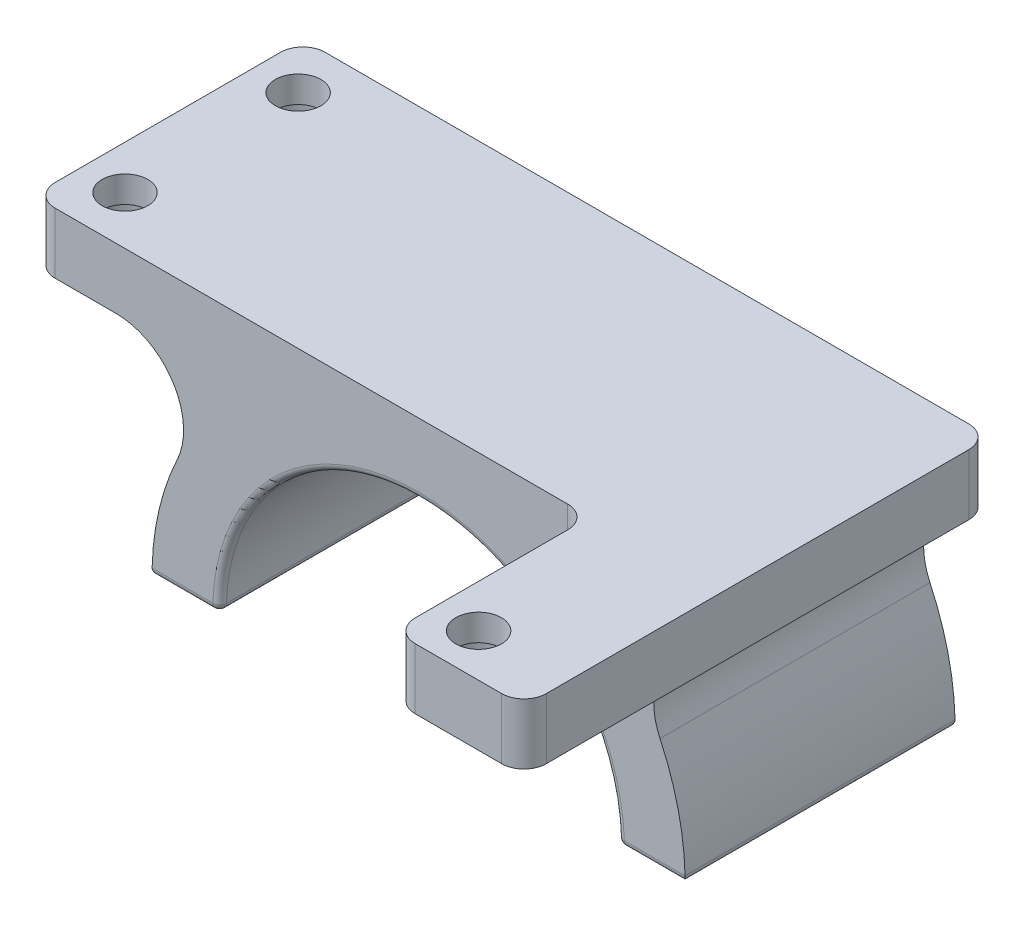
SolidWorks part; units mm, degrees
ref_plane "Front Plane" through (0, 0, 0) normal (0, 0, 1) x (1, 0, 0)
ref_plane "Top Plane" through (0, 0, 0) normal (0, 1, 0) x (1, 0, 0)
ref_plane "Right Plane" through (0, 0, 0) normal (1, 0, 0) x (0, 0, -1)
sketch "Sketch1" plane through (0, 0, 0) normal (0, 0, 1) x (1, 0, 0)
  circle A0 centre (0, 0) radius 39.5
  dimension "D1" = 79
extrude "Boss-Extrude1" add sketch "Sketch1" along normal blind 40 contours A0
sketch "Sketch2" plane through (0, 0, 0) normal (0, 0, -1) x (-1, 0, 0)
  line L0 (-39.5, 0) -> (39.5, 0)
  circle A0 centre (0, 0) radius 39.5 construction
  arc A2 (39.5, 0) -> (-39.5, 0) centre (0, 0) cw
extrude "Cut-Extrude2" cut sketch "Sketch2" against normal through all contours A2 L0
sketch "Sketch3" plane through (0, 0, 0) normal (0, 0, -1) x (-1, 0, 0)
  line L0 (-39.5, 0) -> (39.5, 0) construction
  line L1 (-29.5, 0) -> (29.5, 0)
  arc A0 (-29.5, 0) -> (29.5, 0) centre (0, 0) cw
  dimension "D1" = 29.5
extrude "Cut-Extrude3" cut sketch "Sketch3" against normal through all
fillet "Fillet2" radius 1 10 edges at (29.5, 0, 20) (-29.5, 0, 20) (0, 29.5, 40) (0, 29.5, 0) (-39.5, 0, 20) (39.5, 0, 20) (34.5, 0, 40) (-34.5, 0, 40) (34.5, 0, 0) (-34.5, 0, 0)
sketch "Sketch6" plane through (0, 0, 0) normal (0, 0, -1) x (-1, 0, 0)
  line L5 (-57.15, 40) -> (57.15, 40)
  line L6 (-57.15, 40) -> (-57.15, 31)
  line L7 (-57.15, 31) -> (57.15, 31)
  line L8 (57.15, 40) -> (57.15, 31)
  arc A0 (39.4867, 1.026) -> (-39.4867, 1.026) centre (0, 0) ccw construction
  point P9 (0, 39.5)
  point P10 (0, 31)
  dimension "D3" = 40
  dimension "D1" = 9
  dimension "D2" = 114.3
extrude "Boss-Extrude2" add sketch "Sketch6" against normal up to surface (40 mm away) up to face at (0, 12.3377, 40)
fillet "Fillet6" radius 10 2 edges at (-24.4796, 31, 20) (24.4796, 31, 20)
ref_plane "Plane1" through (-44.8247, 31, 0) normal (-1, 0, 0) x (0, 0, 1)
sketch "Sketch9" plane through (0, 40, 0) normal (0, 1, 0) x (1, 0, 0)
  line L1 (-50.6774, -7.173) -> (-50.6774, -3.7948) construction
  line L4 (-57.15, -40) -> (-57.15, 0) construction
  line L5 (-50.6774, -7.173) -> (-50.6774, -32.827) construction
  circle A0 centre (-50.6774, -7.173) radius 3.3782
  circle A1 centre (-50.6774, -32.827) radius 3.3782
  point P5 (-50.6774, -20)
  point P6 (-57.15, -20)
  dimension "D1" = 6.7564
  dimension "D2" = 6.4726
  dimension "D3" = 2
extrude "Cut-Extrude4" cut sketch "Sketch9" against normal up to surface (10.8916 mm away)
sketch "Sketch10" plane through (0, 40, 0) normal (0, 1, 0) x (1, 0, 0)
  line L0 (57.15, -40) -> (57.15, 0) construction
  circle A0 centre (50.8, -23.937) radius 3.3782
  circle A1 centre (50.8, -61.529) radius 3.3782
  circle A3 centre (-50.6774, -7.173) radius 3.3782 construction
  dimension "D1" = 6.7564
  dimension "D3" = 16.764
  dimension "D4" = 6.35
  dimension "D2" = 2
sketch "Sketch11" plane through (0, 0, 40) normal (0, 0, 1) x (1, 0, 0)
  line L0 (-57.15, 40) -> (57.15, 40) construction
  line L1 (25.4, 40) -> (57.15, 40)
  line L2 (25.4, 40) -> (25.4, 31)
  line L3 (25.4, 31) -> (57.15, 31)
  line L4 (57.15, 40) -> (57.15, 31)
  dimension "D1" = 31.75
extrude "Boss-Extrude3" add sketch "Sketch11" along normal blind 29.21
sketch "Sketch12" plane through (0, 40, 0) normal (0, 1, 0) x (1, 0, 0)
  circle A0 centre (50.8, -23.937) radius 3.3782 construction
  circle A1 centre (50.8, -23.937) radius 3.3782
  circle A2 centre (50.8, -61.529) radius 3.3782 construction
  circle A3 centre (50.8, -61.529) radius 3.3782
sketch "Sketch4" plane through (0, 0, 0) normal (0, -1, 0) x (1, 0, 0)
  line L0 (38.487, 40) -> (30.5, 40) construction
  line L1 (32.9841, 35) -> (35.987, 35)
  line L2 (32.9841, 35) -> (32.9841, 5)
  line L3 (32.9841, 5) -> (35.987, 5)
  line L4 (35.987, 35) -> (35.987, 5)
  line L5 (38.487, 0) -> (-30.5, 0) construction
  line L7 (39.487, 0) -> (39.487, 40) construction
  line L8 (29.4841, 1) -> (29.4841, 39) construction
  line L9 (0, 0) -> (0, 64.0682) construction
  dimension "D1" = 5
  dimension "D2" = 5
  dimension "D3" = 3.5
  dimension "D4" = 3.5
revolve "Cut-Revolve1" cut sketch "Sketch4" angle 360 about L9
fillet "Fillet7" radius 3.302 6 edges at (-57.15, 35.5, 40) (-57.15, 35.5, 0) (57.15, 35.5, 69.21) (57.15, 35.5, 0) (25.4, 35.5, 69.21) (25.4, 35.5, 40)
sketch "Sketch13" plane through (0, 31, 0) normal (0, -1, 0) x (1, 0, 0)
  circle A0 centre (-50.6774, 32.827) radius 5.08
  circle A1 centre (-50.6774, 32.827) radius 3.3782 construction
  circle A2 centre (-50.6774, 7.173) radius 5.08
  dimension "D1" = 10.16
  dimension "D2" = 2
extrude "Cut-Extrude6" cut sketch "Sketch13" against normal blind 5.08
sketch "Sketch14" plane through (0, 31, 0) normal (0, -1, 0) x (1, 0, 0)
  circle A0 centre (50.8, 61.529) radius 5.08
  circle A1 centre (50.8, 24.191) radius 5.08
  dimension "D1" = 10.16
  dimension "D2" = 2
sketch "Sketch15" plane through (0, 31, 0) normal (0, -1, 0) x (1, 0, 0)
  line L0 (25.4, 65.908) -> (25.4, 43.302) construction
  line L2 (28.702, 69.21) -> (53.848, 69.21) construction
  circle A0 centre (31.75, 62.86) radius 3.3782
  point P4 (0, 0)
  point P6 (32.1685, 69.21)
  dimension "D1" = 6.7564
  dimension "D2" = 6.35
  dimension "D3" = 6.35
extrude "Cut-Extrude8" cut sketch "Sketch15" against normal through all
sketch "Sketch16" plane through (0, 31, 0) normal (0, -1, 0) x (1, 0, 0)
  circle A0 centre (31.75, 62.86) radius 5.08
  circle A1 centre (31.75, 62.86) radius 3.3782 construction
  dimension "D1" = 10.16
extrude "Cut-Extrude9" cut sketch "Sketch16" against normal blind 5.08
sketch "Sketch17" plane through (0, 31, 0) normal (0, -1, 0) x (1, 0, 0)
  line L1 (44.8247, 0) -> (81.4109, 0)
  line L2 (44.8247, 0) -> (44.8247, 70.8356)
  line L3 (44.8247, 70.8356) -> (81.4109, 70.8356)
  line L4 (81.4109, 0) -> (81.4109, 70.8356)
extrude "Cut-Extrude10" cut sketch "Sketch17" against normal through all
fillet "Fillet8" radius 3.302 2 edges at (44.8247, 35.5, 69.21) (44.8247, 35.5, 0)
